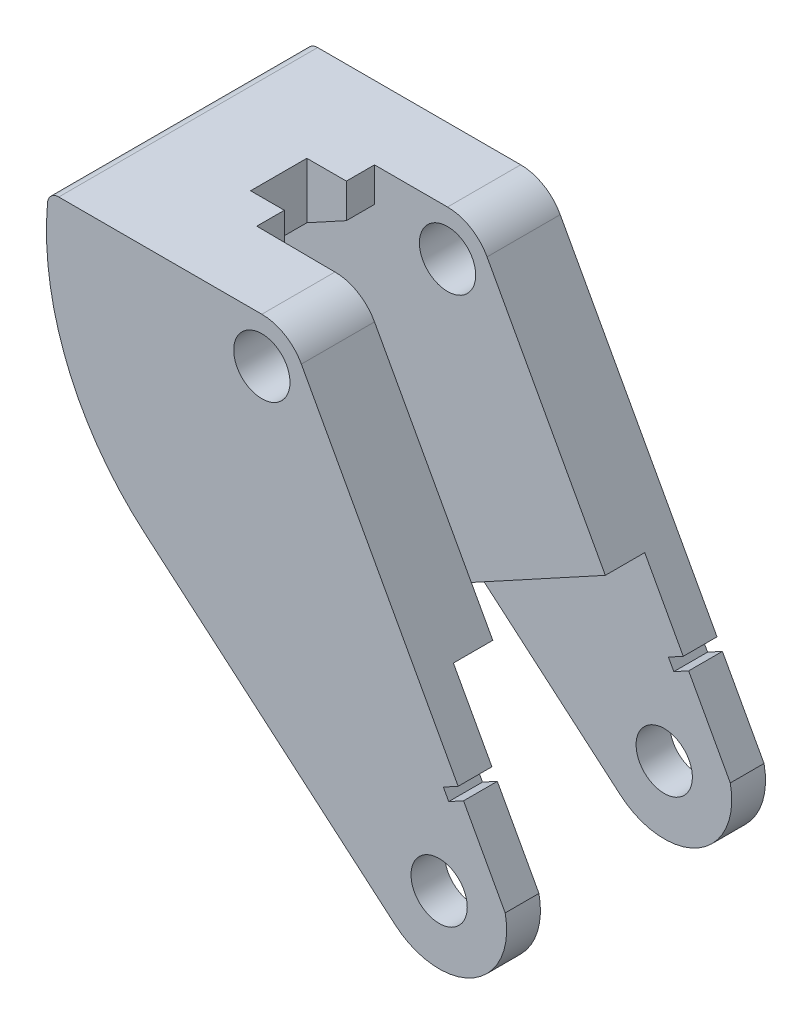
SolidWorks part; units mm, degrees
material "AISI 1020 Steel, Cold Rolled"
ref_plane "Front Plane" through (0, 0, 0) normal (0, 0, 1) x (1, 0, 0)
ref_plane "Top Plane" through (0, 0, 0) normal (0, 1, 0) x (1, 0, 0)
ref_plane "Right Plane" through (0, 0, 0) normal (1, 0, 0) x (0, 0, -1)
sketch "Sketch3" plane through (0, 0, 0) normal (0, 0, 1) x (1, 0, 0)
  line L0 (0, 0) -> (40.8834, 0)
  line L1 (20.054, -44.0776) -> (64.5955, -82.1244)
  line L2 (84.1286, -70.5116) -> (47.905, -4.1663)
  line L3 (75.7704, -55.2032) -> (73.1373, -56.6409)
  line L4 (40.8834, -8) -> (-108.1596, 8.4195)
  line L5 (-108.1596, 8.4195) -> (-107.4053, 8.9224)
  line L6 (18.1599, -8) -> (63.9818, -8) construction
  line L8 (73.1373, -56.6409) -> (74.0958, -58.3963)
  line L9 (74.0958, -58.3963) -> (76.7289, -56.9586)
  arc A1 (0, 0) -> (20.054, -44.0776) centre (40.8834, -8) ccw
  arc A2 (64.5955, -82.1244) -> (84.1286, -70.5116) centre (72.3894, -73) ccw
  arc A3 (40.8834, 0) -> (47.905, -4.1663) centre (40.8834, -8) cw
  circle A4 centre (40.8834, -8) radius 5
  circle A5 centre (72.3894, -73) radius 5
  arc A6 (3, 0) -> (20.054, -44.0776) centre (52.3815, -6.2318) ccw
  point P5 (3, 0)
  dimension "D3" = 12
  dimension "D4" = 8
  dimension "D5" = 10
  dimension "D6" = 10
  dimension "D2" = 3
  dimension "D7" = 65
  dimension "D8" = 3
  dimension "D9" = 2
  dimension "D10" = 12
extrude "Boss-Extrude1" add sketch "Sketch3" along normal blind 46
sketch "Sketch4" plane through (35.1516, 19.1923, 0) normal (0.8777, 0.4792, 0) x (0, 0, -1)
  line L0 (-40, -114.237) -> (-40, -70.4757)
  line L3 (-6, -70.4757) -> (-6, -114.237)
  line L4 (-46, -102.2034) -> (-46, -86.7619) construction
  line L5 (-40, -114.237) -> (-6, -114.237)
  line L8 (-13, -18.717) -> (-33, -18.717)
  line L13 (-6, -70.4757) -> (-13, -70.4757)
  line L14 (-13, -70.4757) -> (-13, -18.717)
  line L15 (-40, -70.4757) -> (-33, -70.4757)
  line L16 (-33, -70.4757) -> (-33, -18.717)
  line L17 (-23, -26.6134) -> (-23, -127.2182) construction
  line L18 (-46, -26.6134) -> (0, -26.6134) construction
  dimension "D1" = 6
  dimension "D2" = 17
  dimension "D3" = 20
  dimension "D4" = 7
extrude "Cut-Extrude1" cut sketch "Sketch4" against normal blind 300
sketch "Sketch5" plane through (0, 0, 0) normal (0, 1, 0) x (1, 0, 0)
  line L0 (39.0579, -13) -> (27.9042, -13)
  line L1 (27.9042, -13) -> (27.9042, -18)
  line L2 (27.9042, -18) -> (20.8834, -18)
  line L3 (20.8834, -18) -> (20.8834, -28)
  line L4 (20.8834, -28) -> (26.8834, -28)
  line L5 (26.8834, -28) -> (26.8834, -32.8934)
  line L6 (26.8834, -32.8934) -> (39.0579, -33)
  line L7 (39.0579, -23) -> (-2.2368, -23) construction
  line L8 (39.0579, -13) -> (39.0579, -33) construction
  line L9 (39.0579, -13) -> (39.0579, -33)
  line L10 (40.8834, -46) -> (40.8834, -33) construction
  dimension "D1" = 10
  dimension "D2" = 5
  dimension "D3" = 4.8934
  dimension "D4" = 20
  dimension "D5" = 14
extrude "Cut-Extrude2" cut sketch "Sketch5" against normal blind 300
fillet "Fillet1" radius 2 1 edges at (3, 0, 23)
